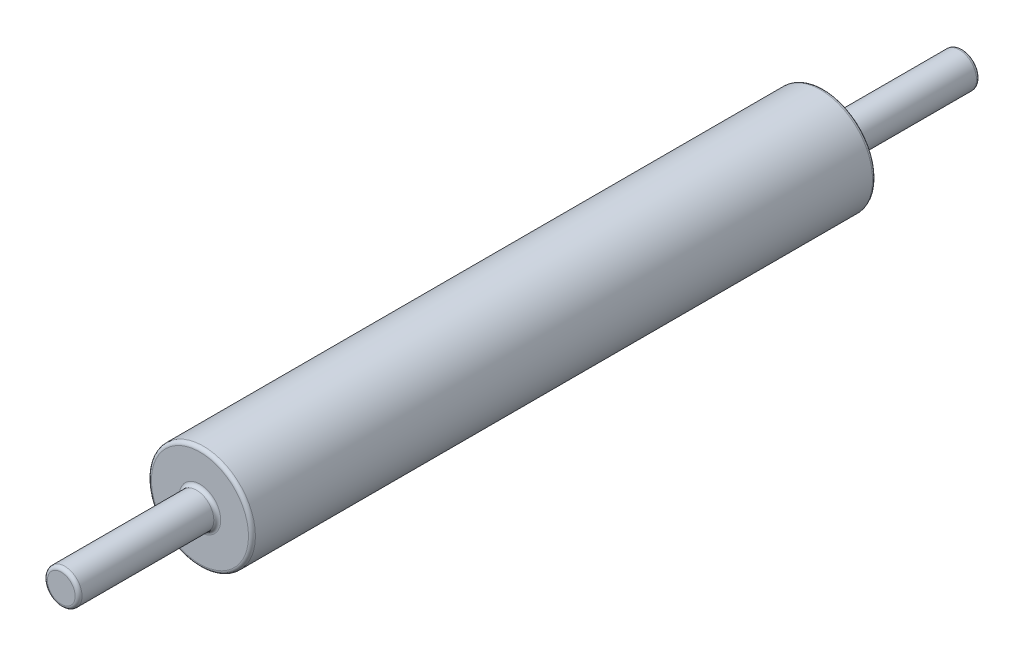
SolidWorks part; units mm, degrees
ref_plane "Front Plane" through (0, 0, 0) normal (0, 0, 1) x (1, 0, 0)
ref_plane "Top Plane" through (0, 0, 0) normal (0, 1, 0) x (1, 0, 0)
ref_plane "Right Plane" through (0, 0, 0) normal (1, 0, 0) x (0, 0, -1)
sketch "Sketch1" plane through (0, 0, 0) normal (0, 0, 1) x (1, 0, 0)
  circle A0 centre (0, 0) radius 38.1
  dimension "D1" = 76.2
extrude "Boss-Extrude1" add sketch "Sketch1" along normal blind 457.2
sketch "Sketch2" plane through (0, 0, 0) normal (0, 0, -1) x (-1, 0, 0)
  circle A0 centre (0, 0) radius 12.7
  dimension "D1" = 25.4
extrude "Boss-Extrude2" add sketch "Sketch2" along normal blind 101.6
sketch "Sketch3" plane through (0, 0, 457.2) normal (0, 0, 1) x (1, 0, 0)
  circle A0 centre (0, 0) radius 12.7
  dimension "D1" = 25.4
extrude "Boss-Extrude3" add sketch "Sketch3" along normal blind 101.6
fillet "Fillet1" radius 2.54 2 edges at (-12.7, 0, 0) (12.7, 0, 457.2)
fillet "Fillet2" radius 2.54 4 edges at (12.7, 0, 558.8) (-12.7, 0, -101.6) (38.1, 0, 0) (38.1, 0, 457.2)
